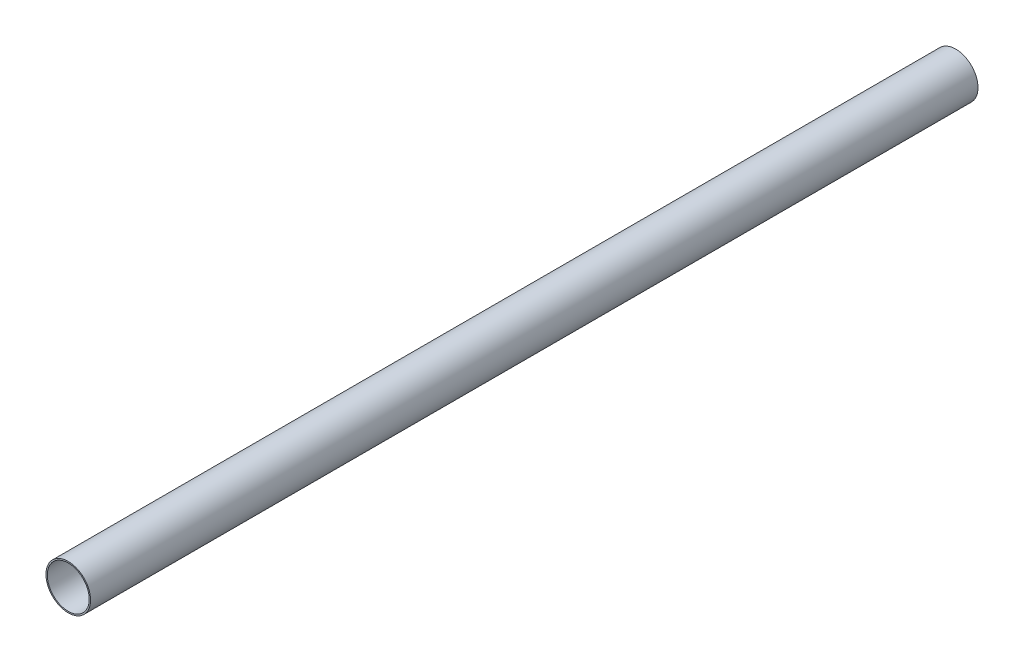
SolidWorks part; units mm, degrees
material "6061-T6 (SS)"
ref_plane "Front Plane" through (0, 0, 0) normal (0, 0, 1) x (1, 0, 0)
ref_plane "Top Plane" through (0, 0, 0) normal (0, 1, 0) x (1, 0, 0)
ref_plane "Right Plane" through (0, 0, 0) normal (1, 0, 0) x (0, 0, -1)
sketch "Sketch2" plane through (0, 0, 0) normal (0, 0, 1) x (1, 0, 0)
  circle A0 centre (0, 0) radius 25
  circle A1 centre (0, 0) radius 23.5
extrude "Boss-Extrude1" add sketch "Sketch2" along normal blind 995
